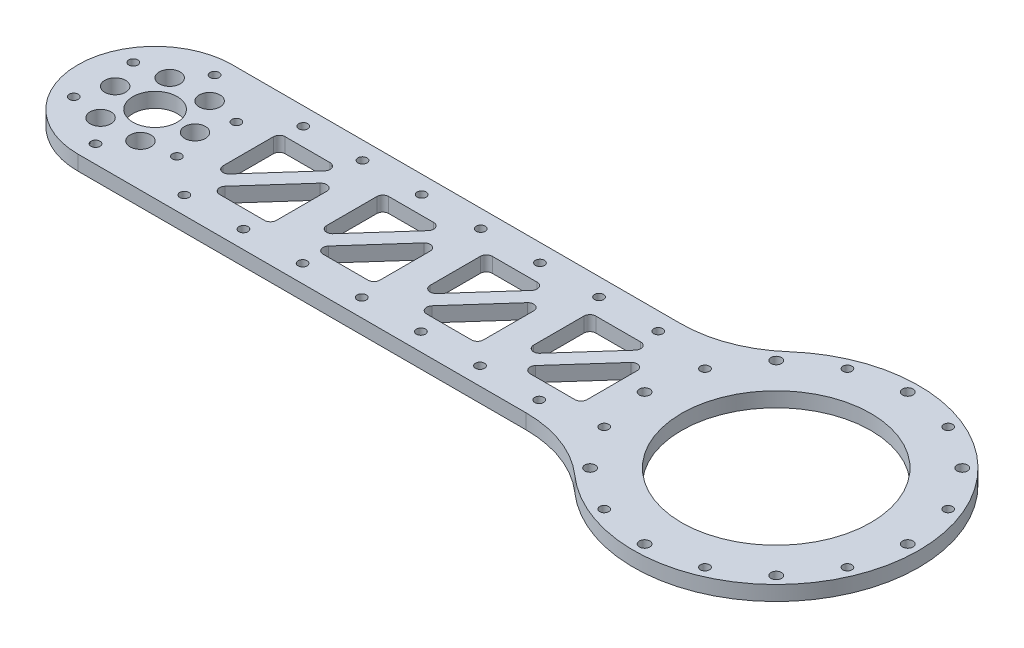
SolidWorks part; units mm, degrees
material "Thornel Mat VMA"
ref_plane "前视基准面" through (0, 0, 0) normal (0, 0, 1) x (1, 0, 0)
ref_plane "上视基准面" through (0, 0, 0) normal (0, 1, 0) x (1, 0, 0)
ref_plane "右视基准面" through (0, 0, 0) normal (1, 0, 0) x (0, 0, -1)
other "Configuration Table"
sketch "草图1" plane through (0, 0, 0) normal (0, 1, 0) x (1, 0, 0)
  line L1 (-105, -26.125) -> (105, -26.125)
  line L2 (-105, -26.125) -> (-105, 26.125)
  line L3 (-105, 26.125) -> (105, 26.125)
  line L4 (105, -26.125) -> (105, 26.125)
  line L5 (-105, -26.125) -> (105, 26.125) construction
  line L6 (-105, 26.125) -> (105, -26.125) construction
  circle A0 centre (-105, 0) radius 26.125
  point P0 (0, 0)
  dimension "D1" = 52.25
  dimension "D2" = 210
extrude "凸台-拉伸1" add sketch "草图1" along normal blind 5 contours A0 L1 L4 L3 | L2 A0 | L2 A0
sketch "草图2" plane through (0, 5, 0) normal (0, 1, 0) x (1, 0, 0)
  circle A0 centre (-105, 0) radius 13.5 construction
  circle A1 centre (-91.5, 0) radius 1.525
  circle A2 centre (-98.25, -11.6913) radius 1.525
  circle A3 centre (-111.75, -11.6913) radius 1.525
  circle A4 centre (-118.5, 0) radius 1.525
  circle A5 centre (-111.75, 11.6913) radius 1.525
  circle A6 centre (-98.25, 11.6913) radius 1.525
  point P17 (-105, 0)
  dimension "D1" = 27
  dimension "D2" = 3.05
  dimension "D3" = 6
extrude "切除-拉伸1" cut sketch "草图2" against normal through all
sketch "草图3" plane through (0, 5, 0) normal (0, 1, 0) x (1, 0, 0)
  line L0 (105, -26.125) -> (105, 26.125) construction
  circle A0 centre (105, 0) radius 48.25
  dimension "D1" = 96.5
extrude "凸台-拉伸2" add sketch "草图3" against normal up to surface (5 mm away) up to face at (-91.5, 0, 1.525)
sketch "草图4" plane through (0, 5, 0) normal (0, 1, 0) x (1, 0, 0)
  circle A0 centre (105, 0) radius 32
  dimension "D1" = 64
extrude "切除-拉伸2" cut sketch "草图4" against normal through all
sketch "草图5" plane through (0, 5, 0) normal (0, 1, 0) x (1, 0, 0)
  circle A0 centre (105, 0) radius 25 construction
  circle A2 centre (130, 0) radius 1.525
  circle A3 centre (117.5, -21.6506) radius 1.525
  circle A4 centre (92.5, -21.6506) radius 1.525
  circle A5 centre (80, 0) radius 1.525
  circle A6 centre (92.5, 21.6506) radius 1.525
  circle A7 centre (117.5, 21.6506) radius 1.525
  point P25 (105, 0)
  dimension "D1" = 50
  dimension "D2" = 3.05
  dimension "D3" = 6
fillet "圆角1" radius 40 2 edges at (64.4347, 2.5, -26.125) (64.4347, 2.5, 26.125)
sketch "草图9" plane through (0, 5, 0) normal (0, 1, 0) x (1, 0, 0)
  circle A0 centre (-105, 0) radius 7.5
  dimension "D1" = 15
extrude "切除-拉伸7" cut sketch "草图9" against normal through all
sketch "草图10" plane through (0, 5, 0) normal (0, 1, 0) x (1, 0, 0)
  circle A0 centre (105, 0) radius 44.5 construction
  circle A1 centre (149.5, 0) radius 1.775
  circle A2 centre (136.4663, -31.4663) radius 1.775
  circle A3 centre (105, -44.5) radius 1.775
  circle A4 centre (73.5337, -31.4663) radius 1.775
  circle A5 centre (60.5, 0) radius 1.775
  circle A6 centre (73.5337, 31.4663) radius 1.775
  circle A7 centre (105, 44.5) radius 1.775
  circle A8 centre (136.4663, 31.4663) radius 1.775
  point P21 (105, 0)
  dimension "D1" = 89
  dimension "D2" = 3.55
  dimension "D3" = 8
extrude "切除-拉伸8" cut sketch "草图10" against normal through all contours A6 | A5 | A4 | A2 | A8 | A1 | A3 | A7
sketch "草图11" plane through (0, 5, 0) normal (0, 1, 0) x (1, 0, 0)
  line L0 (105, 44.5) -> (105, 0) construction
  line L1 (105, 0) -> (122.0294, 41.1126) construction
  circle A0 centre (105, 0) radius 44.5 construction
  circle A1 centre (122.0294, 41.1126) radius 1.525
  circle A2 centre (146.1126, 17.0294) radius 1.525
  circle A3 centre (146.1126, -17.0294) radius 1.525
  circle A4 centre (122.0294, -41.1126) radius 1.525
  circle A5 centre (87.9706, -41.1126) radius 1.525
  circle A6 centre (63.8874, -17.0294) radius 1.525
  circle A7 centre (63.8874, 17.0294) radius 1.525
  circle A8 centre (87.9706, 41.1126) radius 1.525
  point P23 (105, 0)
  dimension "D1" = 3.05
  dimension "D2" = 22.5
  dimension "D3" = 8
extrude "切除-拉伸9" cut sketch "草图11" against normal through all
sketch "草图15" plane through (0, 5, 0) normal (0, 1, 0) x (1, 0, 0)
  line L0 (-105, 0) -> (-122.4288, 10.0625) construction
  line L1 (-105, 0) -> (-105, 26.125) construction
  line L3 (-105, 26.125) -> (46.5573, 26.125) construction
  circle A0 centre (-105, 0) radius 20.125 construction
  circle A1 centre (-122.4288, 10.0625) radius 1.525
  circle A2 centre (-105, 20.125) radius 1.525
  circle A3 centre (-87.5712, 10.0625) radius 1.525
  circle A4 centre (-87.5712, -10.0625) radius 1.525
  circle A5 centre (-105, -20.125) radius 1.525
  circle A6 centre (-122.4288, -10.0625) radius 1.525
  point P19 (-105, 0)
  dimension "D1" = 6
  dimension "D2" = 3.05
  dimension "D3" = 60
  dimension "D4" = 6
extrude "切除-拉伸10" cut sketch "草图15" against normal through all
sketch "草图16" plane through (0, 5, 0) normal (0, 1, 0) x (1, 0, 0)
  circle A0 centre (-118.5, 0) radius 1.525 construction
  circle A1 centre (-111.75, -11.6913) radius 1.525 construction
  circle A2 centre (-98.25, -11.6913) radius 1.525 construction
  circle A3 centre (-91.5, 0) radius 1.525 construction
  circle A4 centre (-98.25, 11.6913) radius 1.525 construction
  circle A5 centre (-111.75, 11.6913) radius 1.525 construction
  circle A6 centre (-118.5, 0) radius 1.525 construction
  circle A7 centre (-111.75, -11.6913) radius 1.525 construction
  circle A8 centre (-98.25, -11.6913) radius 1.525 construction
  circle A9 centre (-91.5, 0) radius 1.525 construction
  circle A10 centre (-98.25, 11.6913) radius 1.525 construction
  circle A11 centre (-111.75, 11.6913) radius 1.525 construction
  circle A12 centre (-118.5, 0) radius 3.525
  circle A13 centre (-111.75, -11.6913) radius 3.525
  circle A14 centre (-98.25, -11.6913) radius 3.525
  circle A15 centre (-91.5, 0) radius 3.525
  circle A16 centre (-98.25, 11.6913) radius 3.525
  circle A17 centre (-111.75, 11.6913) radius 3.525
  circle A18 centre (-118.5, 0) radius 0.525 construction
  circle A19 centre (-111.75, -11.6913) radius 0.525 construction
  circle A20 centre (-98.25, -11.6913) radius 0.525 construction
  circle A21 centre (-91.5, 0) radius 0.525 construction
  circle A22 centre (-98.25, 11.6913) radius 0.525 construction
  circle A23 centre (-111.75, 11.6913) radius 0.525 construction
  dimension "D1" = 2
  dimension "D2" = 1
extrude "切除-拉伸11" cut sketch "草图16" against normal through all
sketch "草图17" plane through (0, 5, 0) normal (0, 1, 0) x (1, 0, 0)
  circle A0 centre (105, 0) radius 42.5 construction
  circle A1 centre (105, 42.5) radius 1.775
  circle A2 centre (105, -42.5) radius 1.775
  dimension "D1" = 85
  dimension "D2" = 3.55
sketch "草图18" plane through (0, 5, 0) normal (0, 1, 0) x (1, 0, 0)
  line L0 (-105, 26.125) -> (46.5573, 26.125) construction
  circle A0 centre (45, 20.125) radius 1.525
  circle A1 centre (25, 20.125) radius 1.525
  circle A2 centre (5, 20.125) radius 1.525
  circle A3 centre (-15, 20.125) radius 1.525
  circle A4 centre (-35, 20.125) radius 1.525
  circle A5 centre (-55, 20.125) radius 1.525
  circle A6 centre (-75, 20.125) radius 1.525
  dimension "D3" = 3.05
  dimension "D1" = 6
  dimension "D2" = 60
  dimension "D5" = 20
  dimension "D4" = 7
extrude "切除-拉伸13" cut sketch "草图18" against normal through all
mirror "镜向1" about plane through (0, 0, 0) normal (0, 0, 1) of "切除-拉伸13"
sketch "草图19" plane through (0, 5, 0) normal (0, 1, 0) x (1, 0, 0)
  line L0 (0, 0) -> (50000, 0) construction
  line L1 (-75.1352, -15.665) -> (-50.1352, 12.335)
  line L2 (-77, -14) -> (-52, -14)
  line L3 (-77, -14) -> (-77, 14)
  line L4 (-77, 14) -> (-52, 14)
  line L5 (-52, -14) -> (-52, 14)
  line L6 (-77, -14) -> (-52, 14) construction
  line L7 (-77, 14) -> (-52, -14) construction
  line L12 (-78.8648, -12.335) -> (-53.8648, 15.665)
  circle A0 centre (-105, 0) radius 7.5 construction
  point P3 (-64.5, 0)
  dimension "D1" = 28
  dimension "D2" = 28
  dimension "D3" = 25
  dimension "D4" = 2.5
  dimension "D5" = 2.5
extrude "切除-拉伸14" cut sketch "草图19" against normal through all contours L3 L12 L4 | L2 L5 L1
fillet "圆角2" radius 2 6 edges at (-55.3515, 2.5, -14) (-77, 2.5, 10.2463) (-52, 2.5, -10.2463) (-52, 2.5, 14) (-73.6485, 2.5, 14) (-77, 2.5, -14)
pattern_linear "阵列(线性)1" count 4 spacing 35 along (1, 0, 0) of "切除-拉伸14", "圆角2"
